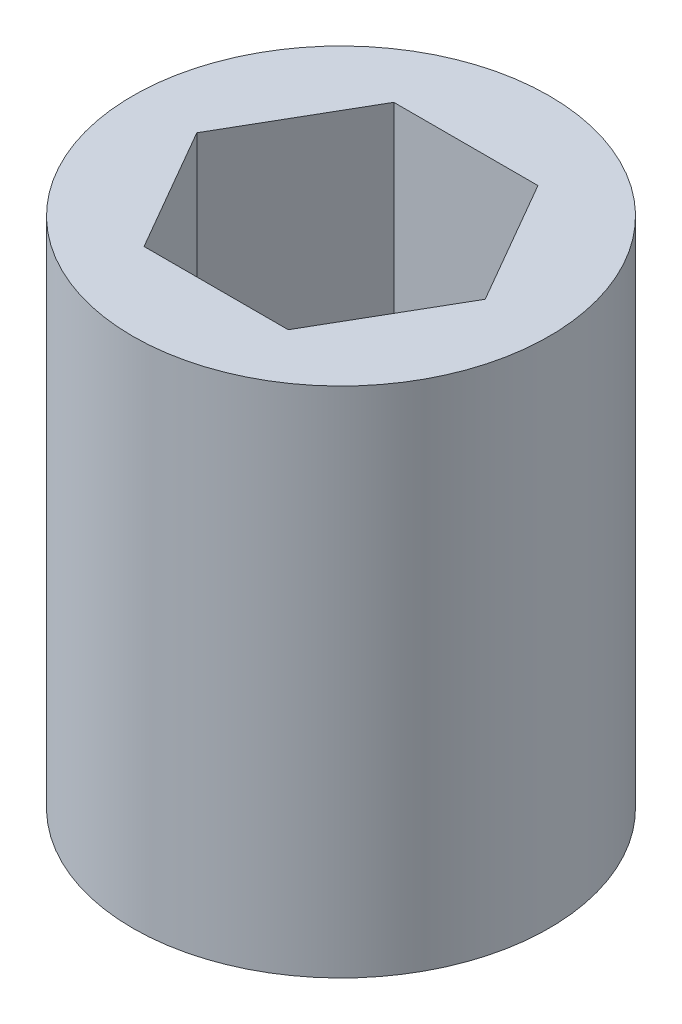
SolidWorks part; units mm, degrees
ref_plane "Front Plane" through (0, 0, 0) normal (0, 0, 1) x (1, 0, 0)
ref_plane "Top Plane" through (0, 0, 0) normal (0, 1, 0) x (1, 0, 0)
ref_plane "Right Plane" through (0, 0, 0) normal (1, 0, 0) x (0, 0, -1)
sketch "Sketch1" plane through (0, 0, 0) normal (0, 1, 0) x (1, 0, 0)
  circle A0 centre (0, 0) radius 1.625
  dimension "D1" = 3.25
extrude "Boss-Extrude1" add sketch "Sketch1" along normal blind 4
sketch "Sketch2" plane through (0, 4, 0) normal (0, 1, 0) x (1, 0, 0)
  line L0 (-1.625, 0) -> (1.625, 0) construction
  line L1 (1.125, 0) -> (0.5625, 0.9743)
  line L2 (0.5625, 0.9743) -> (-0.5625, 0.9743)
  line L3 (-0.5625, 0.9743) -> (-1.125, 0)
  line L4 (-1.125, 0) -> (-0.5625, -0.9743)
  line L5 (-0.5625, -0.9743) -> (0.5625, -0.9743)
  line L6 (0.5625, -0.9743) -> (1.125, 0)
  circle A0 centre (0, 0) radius 0.9743 construction
  circle A3 centre (0, 0) radius 1.625 construction
  dimension "D1" = 0.5
extrude "Cut-Extrude1" cut sketch "Sketch2" against normal blind 3.5
